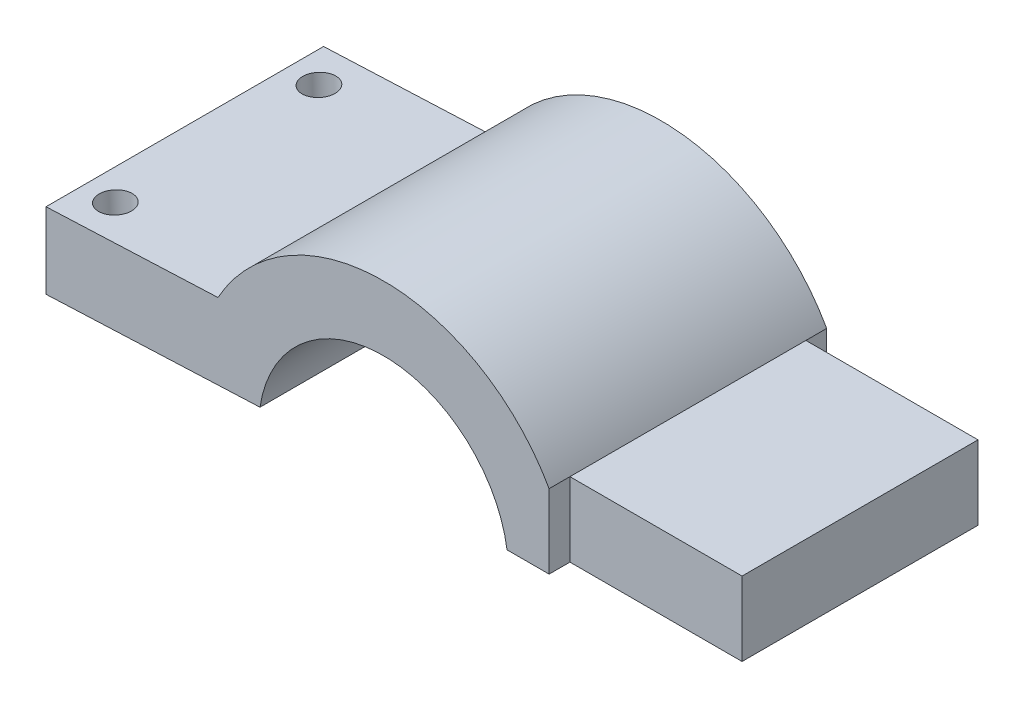
SolidWorks part; units mm, degrees
ref_plane "Alzado" through (0, 0, 0) normal (0, 0, 1) x (1, 0, 0)
ref_plane "Planta" through (0, 0, 0) normal (0, 1, 0) x (1, 0, 0)
ref_plane "Vista lateral" through (0, 0, 0) normal (1, 0, 0) x (0, 0, -1)
sketch "Croquis1" plane through (0, 0, 0) normal (0, 0, 1) x (1, 0, 0)
  line L1 (26.4213, 0) -> (26.4213, 8)
  line L2 (26.4213, 8) -> (7.8169, 8)
  line L4 (3.2724, 0) -> (26.4213, 0)
  line L6 (-23.4297, 0) -> (-46.5584, -0.9936)
  line L7 (-27.9742, 8) -> (-46.5584, 7.2016)
  line L8 (-46.5584, 7.2016) -> (-46.5584, -0.9936)
  arc A0 (3.2724, 0) -> (-23.4297, 0) centre (-10.0787, -2) ccw
  arc A1 (7.8169, 8) -> (-27.9742, 8) centre (-10.0787, -2) ccw
  dimension "D4" = 7
  dimension "D5" = 13.5
  dimension "D1" = 2.46
  dimension "D2" = 8
  dimension "D7" = 23.15
extrude "Saliente-Extruir1" add sketch "Croquis1" along normal blind 30
sketch "Croquis3" plane through (0, 8, 0) normal (0, 1, 0) x (1, 0, 0)
  line L0 (26.4213, -15) -> (19.9915, -15) construction
  line L1 (26.4213, -30) -> (26.4213, 0) construction
  line L2 (26.4213, -2.25) -> (26.4213, -27.75)
  line L3 (26.4213, -27.75) -> (7.8169, -27.75)
  line L4 (7.8169, -30) -> (7.8169, 0) construction
  line L5 (7.8169, -27.75) -> (7.8169, -33.3591)
  line L6 (7.8169, -33.3591) -> (34.2437, -33.3591)
  line L7 (34.2437, -33.3591) -> (34.2437, 4.8571)
  line L8 (34.2437, 4.8571) -> (7.8169, 4.8571)
  line L9 (7.8169, 4.8571) -> (7.8169, -2.25)
  line L10 (7.8169, -2.25) -> (26.4213, -2.25)
  point P7 (26.4213, -15)
  dimension "D1" = 25.5
extrude "Cortar-Extruir1" cut sketch "Croquis3" against normal blind 10
sketch "Croquis4" plane through (-0.3946, 9.1849, 0) normal (-0.0429, 0.9991, 0) x (0.9991, 0.0429, 0)
  line L0 (-27.605, -15) -> (-46.2063, -15) construction
  line L1 (-27.605, -30) -> (-27.605, 0) construction
  line L2 (-46.2063, -30) -> (-46.2063, 0) construction
  circle A0 centre (-42.7063, -26) radius 1.75
  circle A1 centre (-42.7063, -4) radius 1.75
  dimension "D1" = 3.5
  dimension "D2" = 11
  dimension "D3" = 3.5
extrude "Cortar-Extruir2" cut sketch "Croquis4" against normal blind 10
